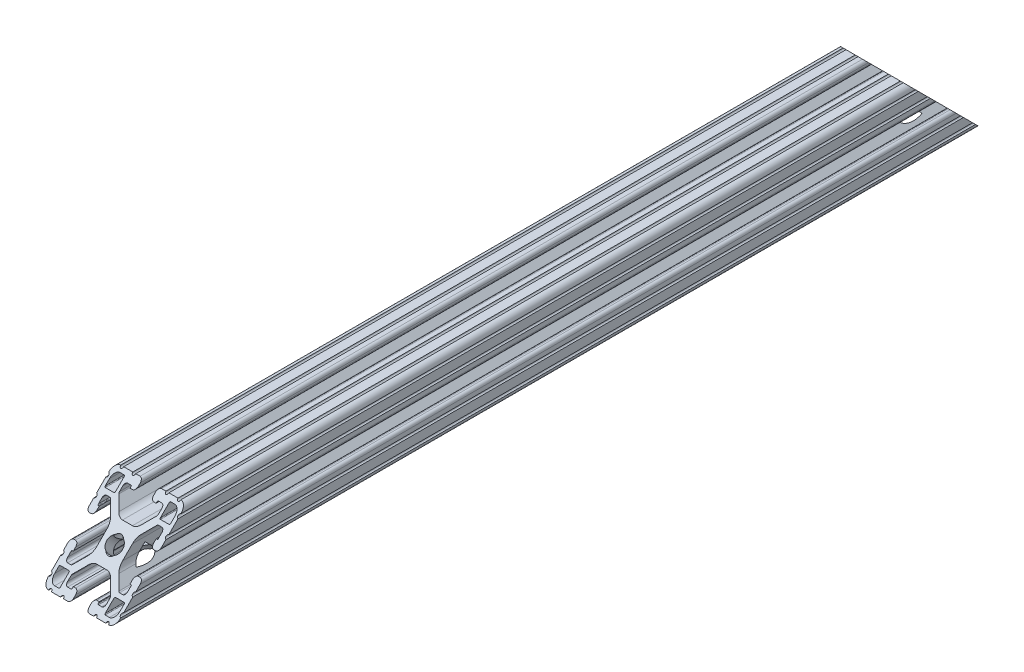
SolidWorks part; units mm, degrees
material "6105-T5 Aluminum"
ref_plane "Front Plane" through (0, 0, 0) normal (0, 0, 1) x (1, 0, 0)
ref_plane "Top Plane" through (0, 0, 0) normal (0, 1, 0) x (1, 0, 0)
ref_plane "Right Plane" through (0, 0, 0) normal (1, 0, 0) x (0, 0, -1)
sketch "Sketch1" plane through (0, 0, 0) normal (0, 0, 1) x (1, 0, 0)
  line L0 (16.8656, 11.8618) -> (12.2428, 11.8618)
  line L1 (11.8618, 12.2428) -> (11.8618, 16.8656)
  line L2 (12.2428, 17.2466) -> (14.4526, 17.2466)
  line L3 (17.2466, 14.4526) -> (17.2466, 12.2428)
  line L4 (-16.8656, -11.8618) -> (-12.2428, -11.8618)
  line L5 (-11.8618, -12.2428) -> (-11.8618, -16.8656)
  line L6 (-12.2428, -17.2466) -> (-14.4526, -17.2466)
  line L7 (-17.2466, -14.4526) -> (-17.2466, -12.2428)
  line L8 (11.8618, -16.8656) -> (11.8618, -12.2428)
  line L9 (12.2428, -11.8618) -> (16.8656, -11.8618)
  line L10 (17.2466, -12.2428) -> (17.2466, -14.4526)
  line L11 (14.4526, -17.2466) -> (12.2428, -17.2466)
  line L12 (-11.8618, 16.8656) -> (-11.8618, 12.2428)
  line L13 (-12.2428, 11.8618) -> (-16.8656, 11.8618)
  line L14 (-17.2466, 12.2428) -> (-17.2466, 14.4526)
  line L15 (-14.4526, 17.2466) -> (-12.2428, 17.2466)
  line L16 (-15.4432, -6.858) -> (-14.986, -6.858)
  line L17 (-14.986, -6.858) -> (-14.986, -5.6388)
  line L18 (-16.5608, -4.064) -> (-17.4752, -4.064)
  line L19 (-19.05, -5.6388) -> (-19.05, -7.9756)
  line L20 (-19.05, -9.4996) -> (-19.05, -14.3256)
  line L21 (-19.05, -15.8496) -> (-19.05, -15.875)
  line L22 (-15.875, -19.05) -> (-15.8496, -19.05)
  line L23 (-14.3256, -19.05) -> (-9.4996, -19.05)
  line L24 (-7.9756, -19.05) -> (-5.6388, -19.05)
  line L25 (-4.064, -17.4752) -> (-4.064, -16.5608)
  line L26 (-5.6388, -14.986) -> (-6.858, -14.986)
  line L27 (-6.858, -14.986) -> (-6.858, -15.4432)
  line L28 (-7.239, -15.8242) -> (-9.017, -15.8242)
  line L29 (-10.287, -14.5542) -> (-10.287, -12.8105)
  line L30 (-10.0266, -12.1819) -> (-5.9739, -8.1292)
  line L31 (-2.6153, -6.738) -> (2.6153, -6.738)
  line L32 (5.9739, -8.1292) -> (10.0266, -12.1819)
  line L33 (10.287, -12.8105) -> (10.287, -14.5542)
  line L34 (9.017, -15.8242) -> (7.239, -15.8242)
  line L35 (6.858, -15.4432) -> (6.858, -14.986)
  line L36 (6.858, -14.986) -> (5.6388, -14.986)
  line L37 (4.064, -16.5608) -> (4.064, -17.4752)
  line L38 (5.6388, -19.05) -> (7.9756, -19.05)
  line L39 (9.4996, -19.05) -> (14.3256, -19.05)
  line L40 (15.8496, -19.05) -> (15.875, -19.05)
  line L41 (19.05, -15.875) -> (19.05, -15.8496)
  line L42 (19.05, -14.3256) -> (19.05, -9.4996)
  line L43 (19.05, -7.9756) -> (19.05, -5.6388)
  line L44 (17.4752, -4.064) -> (16.5608, -4.064)
  line L45 (14.986, -5.6388) -> (14.986, -6.858)
  line L46 (14.986, -6.858) -> (15.4432, -6.858)
  line L47 (15.8242, -7.239) -> (15.8242, -9.017)
  line L48 (14.5542, -10.287) -> (12.8105, -10.287)
  line L49 (12.1819, -10.0266) -> (8.1292, -5.9739)
  line L50 (6.738, -2.6153) -> (6.738, 2.6153)
  line L51 (8.1292, 5.9739) -> (12.1819, 10.0266)
  line L52 (12.8105, 10.287) -> (14.5542, 10.287)
  line L53 (15.8242, 9.017) -> (15.8242, 7.239)
  line L54 (15.4432, 6.858) -> (14.986, 6.858)
  line L55 (14.986, 6.858) -> (14.986, 5.6388)
  line L56 (16.5608, 4.064) -> (17.4752, 4.064)
  line L57 (19.05, 5.6388) -> (19.05, 7.9756)
  line L58 (19.05, 9.4996) -> (19.05, 14.3256)
  line L59 (19.05, 15.8496) -> (19.05, 15.875)
  line L60 (15.875, 19.05) -> (15.8496, 19.05)
  line L61 (14.3256, 19.05) -> (9.4996, 19.05)
  line L62 (7.9756, 19.05) -> (5.6388, 19.05)
  line L63 (4.064, 17.4752) -> (4.064, 16.5608)
  line L64 (5.6388, 14.986) -> (6.858, 14.986)
  line L65 (6.858, 14.986) -> (6.858, 15.4432)
  line L66 (7.239, 15.8242) -> (9.017, 15.8242)
  line L67 (10.287, 14.5542) -> (10.287, 12.8105)
  line L68 (10.0266, 12.1819) -> (5.9739, 8.1292)
  line L69 (2.6153, 6.738) -> (-2.6153, 6.738)
  line L70 (-5.9739, 8.1292) -> (-10.0266, 12.1819)
  line L71 (-10.287, 12.8105) -> (-10.287, 14.5542)
  line L72 (-9.017, 15.8242) -> (-7.239, 15.8242)
  line L73 (-6.858, 15.4432) -> (-6.858, 14.986)
  line L74 (-6.858, 14.986) -> (-5.6388, 14.986)
  line L75 (-4.064, 16.5608) -> (-4.064, 17.4752)
  line L76 (-5.6388, 19.05) -> (-7.9756, 19.05)
  line L77 (-9.4996, 19.05) -> (-14.3256, 19.05)
  line L78 (-15.8496, 19.05) -> (-15.875, 19.05)
  line L79 (-19.05, 15.875) -> (-19.05, 15.8496)
  line L80 (-19.05, 14.3256) -> (-19.05, 9.4996)
  line L81 (-19.05, 7.9756) -> (-19.05, 5.6388)
  line L82 (-17.4752, 4.064) -> (-16.5608, 4.064)
  line L83 (-14.986, 5.6388) -> (-14.986, 6.858)
  line L84 (-14.986, 6.858) -> (-15.4432, 6.858)
  line L85 (-15.8242, 7.239) -> (-15.8242, 9.017)
  line L86 (-14.5542, 10.287) -> (-12.8105, 10.287)
  line L87 (-12.1819, 10.0266) -> (-8.1292, 5.9739)
  line L88 (-6.738, 2.6153) -> (-6.738, -2.6153)
  line L89 (-8.1292, -5.9739) -> (-12.1819, -10.0266)
  line L90 (-12.8105, -10.287) -> (-14.5542, -10.287)
  line L91 (-15.8242, -9.017) -> (-15.8242, -7.239)
  arc A0 (11.8618, 12.2428) -> (12.2428, 11.8618) centre (12.2428, 12.2428) ccw
  arc A1 (12.2428, 17.2466) -> (11.8618, 16.8656) centre (12.2428, 16.8656) ccw
  arc A2 (17.2466, 14.4526) -> (14.4526, 17.2466) centre (14.4526, 14.4526) ccw
  arc A3 (16.8656, 11.8618) -> (17.2466, 12.2428) centre (16.8656, 12.2428) ccw
  arc A4 (-11.8618, -12.2428) -> (-12.2428, -11.8618) centre (-12.2428, -12.2428) ccw
  arc A5 (-12.2428, -17.2466) -> (-11.8618, -16.8656) centre (-12.2428, -16.8656) ccw
  arc A6 (-17.2466, -14.4526) -> (-14.4526, -17.2466) centre (-14.4526, -14.4526) ccw
  arc A7 (-16.8656, -11.8618) -> (-17.2466, -12.2428) centre (-16.8656, -12.2428) ccw
  circle A8 centre (0, 0) radius 3.3274
  arc A9 (12.2428, -11.8618) -> (11.8618, -12.2428) centre (12.2428, -12.2428) ccw
  arc A10 (17.2466, -12.2428) -> (16.8656, -11.8618) centre (16.8656, -12.2428) ccw
  arc A11 (14.4526, -17.2466) -> (17.2466, -14.4526) centre (14.4526, -14.4526) ccw
  arc A12 (11.8618, -16.8656) -> (12.2428, -17.2466) centre (12.2428, -16.8656) ccw
  arc A13 (-12.2428, 11.8618) -> (-11.8618, 12.2428) centre (-12.2428, 12.2428) ccw
  arc A14 (-17.2466, 12.2428) -> (-16.8656, 11.8618) centre (-16.8656, 12.2428) ccw
  arc A15 (-14.4526, 17.2466) -> (-17.2466, 14.4526) centre (-14.4526, 14.4526) ccw
  arc A16 (-11.8618, 16.8656) -> (-12.2428, 17.2466) centre (-12.2428, 16.8656) ccw
  arc A17 (-15.4432, -6.858) -> (-15.8242, -7.239) centre (-15.4432, -7.239) ccw
  arc A18 (-14.986, -5.6388) -> (-16.5608, -4.064) centre (-16.5608, -5.6388) ccw
  arc A19 (-17.4752, -4.064) -> (-19.05, -5.6388) centre (-17.4752, -5.6388) ccw
  arc A20 (-19.05, -9.4996) -> (-19.05, -7.9756) centre (-19.05, -8.7376) ccw
  arc A21 (-19.05, -15.8496) -> (-19.05, -14.3256) centre (-19.05, -15.0876) ccw
  arc A22 (-19.05, -15.875) -> (-15.875, -19.05) centre (-15.875, -15.875) ccw
  arc A23 (-14.3256, -19.05) -> (-15.8496, -19.05) centre (-15.0876, -19.05) ccw
  arc A24 (-7.9756, -19.05) -> (-9.4996, -19.05) centre (-8.7376, -19.05) ccw
  arc A25 (-5.6388, -19.05) -> (-4.064, -17.4752) centre (-5.6388, -17.4752) ccw
  arc A26 (-4.064, -16.5608) -> (-5.6388, -14.986) centre (-5.6388, -16.5608) ccw
  arc A27 (-7.239, -15.8242) -> (-6.858, -15.4432) centre (-7.239, -15.4432) ccw
  arc A28 (-10.287, -14.5542) -> (-9.017, -15.8242) centre (-9.017, -14.5542) ccw
  arc A29 (-10.0266, -12.1819) -> (-10.287, -12.8105) centre (-9.398, -12.8105) ccw
  arc A30 (-2.6153, -6.738) -> (-5.9739, -8.1292) centre (-2.6153, -11.4878) ccw
  arc A31 (5.9739, -8.1292) -> (2.6153, -6.738) centre (2.6153, -11.4878) ccw
  arc A32 (10.287, -12.8105) -> (10.0266, -12.1819) centre (9.398, -12.8105) ccw
  arc A33 (9.017, -15.8242) -> (10.287, -14.5542) centre (9.017, -14.5542) ccw
  arc A34 (6.858, -15.4432) -> (7.239, -15.8242) centre (7.239, -15.4432) ccw
  arc A35 (5.6388, -14.986) -> (4.064, -16.5608) centre (5.6388, -16.5608) ccw
  arc A36 (4.064, -17.4752) -> (5.6388, -19.05) centre (5.6388, -17.4752) ccw
  arc A37 (9.4996, -19.05) -> (7.9756, -19.05) centre (8.7376, -19.05) ccw
  arc A38 (15.8496, -19.05) -> (14.3256, -19.05) centre (15.0876, -19.05) ccw
  arc A39 (15.875, -19.05) -> (19.05, -15.875) centre (15.875, -15.875) ccw
  arc A40 (19.05, -14.3256) -> (19.05, -15.8496) centre (19.05, -15.0876) ccw
  arc A41 (19.05, -7.9756) -> (19.05, -9.4996) centre (19.05, -8.7376) ccw
  arc A42 (19.05, -5.6388) -> (17.4752, -4.064) centre (17.4752, -5.6388) ccw
  arc A43 (16.5608, -4.064) -> (14.986, -5.6388) centre (16.5608, -5.6388) ccw
  arc A44 (15.8242, -7.239) -> (15.4432, -6.858) centre (15.4432, -7.239) ccw
  arc A45 (14.5542, -10.287) -> (15.8242, -9.017) centre (14.5542, -9.017) ccw
  arc A46 (12.1819, -10.0266) -> (12.8105, -10.287) centre (12.8105, -9.398) ccw
  arc A47 (6.738, -2.6153) -> (8.1292, -5.9739) centre (11.4878, -2.6153) ccw
  arc A48 (8.1292, 5.9739) -> (6.738, 2.6153) centre (11.4878, 2.6153) ccw
  arc A49 (12.8105, 10.287) -> (12.1819, 10.0266) centre (12.8105, 9.398) ccw
  arc A50 (15.8242, 9.017) -> (14.5542, 10.287) centre (14.5542, 9.017) ccw
  arc A51 (15.4432, 6.858) -> (15.8242, 7.239) centre (15.4432, 7.239) ccw
  arc A52 (14.986, 5.6388) -> (16.5608, 4.064) centre (16.5608, 5.6388) ccw
  arc A53 (17.4752, 4.064) -> (19.05, 5.6388) centre (17.4752, 5.6388) ccw
  arc A54 (19.05, 9.4996) -> (19.05, 7.9756) centre (19.05, 8.7376) ccw
  arc A55 (19.05, 15.8496) -> (19.05, 14.3256) centre (19.05, 15.0876) ccw
  arc A56 (19.05, 15.875) -> (15.875, 19.05) centre (15.875, 15.875) ccw
  arc A57 (14.3256, 19.05) -> (15.8496, 19.05) centre (15.0876, 19.05) ccw
  arc A58 (7.9756, 19.05) -> (9.4996, 19.05) centre (8.7376, 19.05) ccw
  arc A59 (5.6388, 19.05) -> (4.064, 17.4752) centre (5.6388, 17.4752) ccw
  arc A60 (4.064, 16.5608) -> (5.6388, 14.986) centre (5.6388, 16.5608) ccw
  arc A61 (7.239, 15.8242) -> (6.858, 15.4432) centre (7.239, 15.4432) ccw
  arc A62 (10.287, 14.5542) -> (9.017, 15.8242) centre (9.017, 14.5542) ccw
  arc A63 (10.0266, 12.1819) -> (10.287, 12.8105) centre (9.398, 12.8105) ccw
  arc A64 (2.6153, 6.738) -> (5.9739, 8.1292) centre (2.6153, 11.4878) ccw
  arc A65 (-5.9739, 8.1292) -> (-2.6153, 6.738) centre (-2.6153, 11.4878) ccw
  arc A66 (-10.287, 12.8105) -> (-10.0266, 12.1819) centre (-9.398, 12.8105) ccw
  arc A67 (-9.017, 15.8242) -> (-10.287, 14.5542) centre (-9.017, 14.5542) ccw
  arc A68 (-6.858, 15.4432) -> (-7.239, 15.8242) centre (-7.239, 15.4432) ccw
  arc A69 (-5.6388, 14.986) -> (-4.064, 16.5608) centre (-5.6388, 16.5608) ccw
  arc A70 (-4.064, 17.4752) -> (-5.6388, 19.05) centre (-5.6388, 17.4752) ccw
  arc A71 (-9.4996, 19.05) -> (-7.9756, 19.05) centre (-8.7376, 19.05) ccw
  arc A72 (-15.8496, 19.05) -> (-14.3256, 19.05) centre (-15.0876, 19.05) ccw
  arc A73 (-15.875, 19.05) -> (-19.05, 15.875) centre (-15.875, 15.875) ccw
  arc A74 (-19.05, 14.3256) -> (-19.05, 15.8496) centre (-19.05, 15.0876) ccw
  arc A75 (-19.05, 7.9756) -> (-19.05, 9.4996) centre (-19.05, 8.7376) ccw
  arc A76 (-19.05, 5.6388) -> (-17.4752, 4.064) centre (-17.4752, 5.6388) ccw
  arc A77 (-16.5608, 4.064) -> (-14.986, 5.6388) centre (-16.5608, 5.6388) ccw
  arc A78 (-15.8242, 7.239) -> (-15.4432, 6.858) centre (-15.4432, 7.239) ccw
  arc A79 (-14.5542, 10.287) -> (-15.8242, 9.017) centre (-14.5542, 9.017) ccw
  arc A80 (-12.1819, 10.0266) -> (-12.8105, 10.287) centre (-12.8105, 9.398) ccw
  arc A81 (-6.738, 2.6153) -> (-8.1292, 5.9739) centre (-11.4878, 2.6153) ccw
  arc A82 (-8.1292, -5.9739) -> (-6.738, -2.6153) centre (-11.4878, -2.6153) ccw
  arc A83 (-12.8105, -10.287) -> (-12.1819, -10.0266) centre (-12.8105, -9.398) ccw
  arc A84 (-15.8242, -9.017) -> (-14.5542, -10.287) centre (-14.5542, -9.017) ccw
extrude "Extrude1" add sketch "Sketch1" against normal blind 228.6
sketch "Sketch2" plane through (19.05, 0, 0) normal (1, 0, 0) x (0, 0, -1)
  line L0 (0, -19.05) -> (0, 27.8801)
  line L1 (0, 27.8801) -> (46.9301, 27.8801)
  line L2 (46.9301, 27.8801) -> (0, -19.05)
  dimension "D1" = 45
extrude "Cut-Extrude1" cut sketch "Sketch2" against normal through all
sketch "Sketch3" plane through (0, -9.525, -9.525) normal (0, 0.7071, 0.7071) x (1, 0, 0)
  circle A0 centre (0, 13.4704) radius 4.1656
  dimension "D1" = 8.3312
extrude "Cut-Extrude2" cut sketch "Sketch3" along normal blind 16.764 from offset 6.35 offset against normal yes
sketch "Sketch4" plane through (0, -9.525, -9.525) normal (0, 0.7071, 0.7071) x (1, 0, 0)
  circle A0 centre (0, 13.4704) radius 9.525
  dimension "D1" = 19.05
extrude "Cut-Extrude3" cut sketch "Sketch4" against normal blind 37.592 from offset 6.35 offset against normal yes
mirror "Mirror1" about plane through (-15.4432, -7.239, -228.6) normal (0, 0, 1) of "Cut-Extrude3", "Cut-Extrude2", "Cut-Extrude1", "Extrude1"
